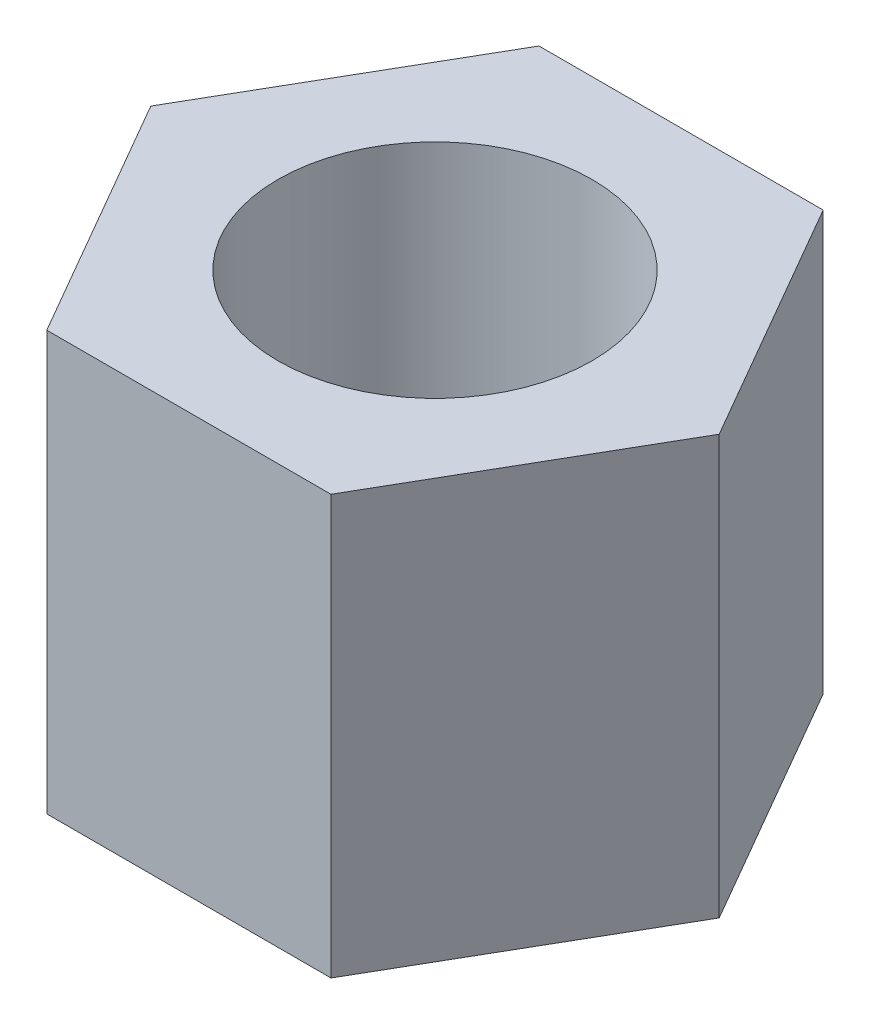
SolidWorks part; units mm, degrees
ref_plane "前视基准面" through (0, 0, 0) normal (0, 0, 1) x (1, 0, 0)
ref_plane "上视基准面" through (0, 0, 0) normal (0, 1, 0) x (1, 0, 0)
ref_plane "右视基准面" through (0, 0, 0) normal (1, 0, 0) x (0, 0, -1)
sketch "草图1" plane through (0, 0, 0) normal (0, 1, 0) x (1, 0, 0)
  line L1 (2.7135, 0) -> (1.3568, 2.35)
  line L2 (1.3568, 2.35) -> (-1.3568, 2.35)
  line L3 (-1.3568, 2.35) -> (-2.7135, 0)
  line L4 (-2.7135, 0) -> (-1.3568, -2.35)
  line L5 (-1.3568, -2.35) -> (1.3568, -2.35)
  line L6 (1.3568, -2.35) -> (2.7135, 0)
  circle A0 centre (0, 0) radius 2.35 construction
  dimension "D1" = 4.7
extrude "凸台-拉伸1" add sketch "草图1" along normal blind 4
sketch "草图2" plane through (0, 4, 0) normal (0, 1, 0) x (1, 0, 0)
  circle A0 centre (0, 0) radius 1.5
  dimension "D1" = 3
extrude "切除-拉伸1" cut sketch "草图2" against normal through all
